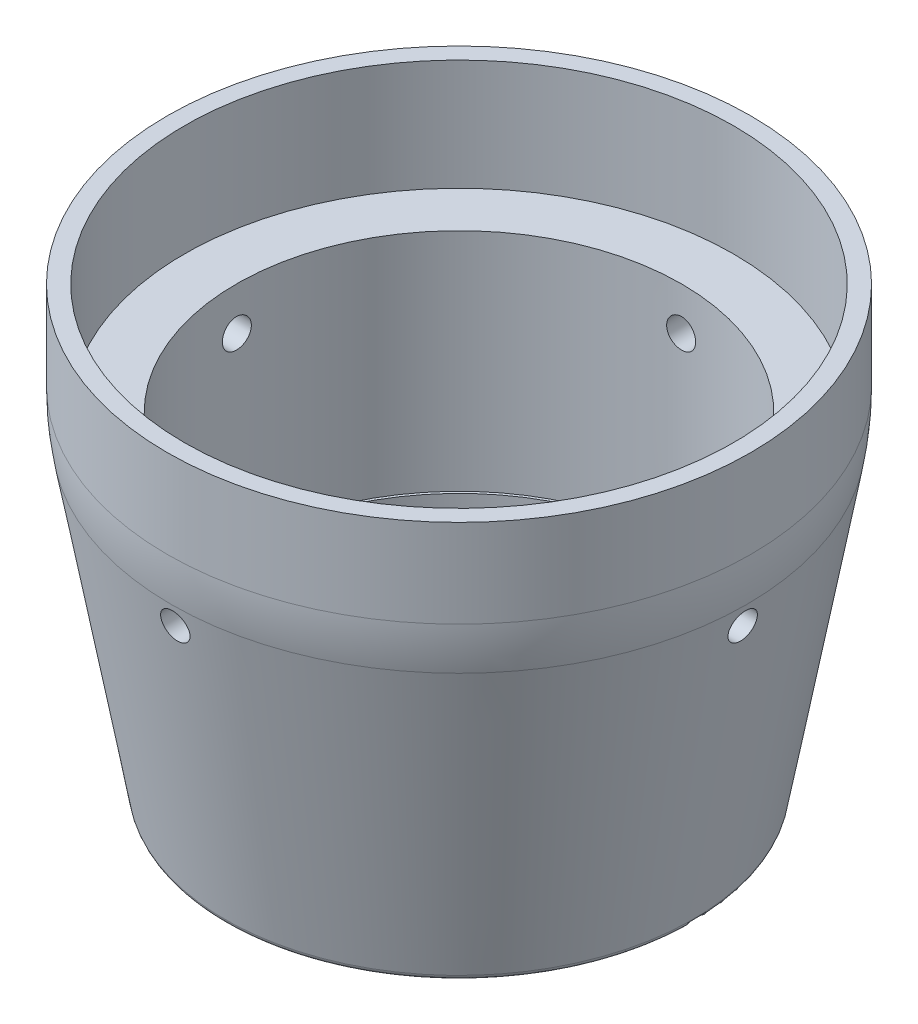
SolidWorks part; units mm, degrees
material "6061-T6 (SS)"
ref_plane "Front Plane" through (0, 0, 0) normal (0, 0, 1) x (1, 0, 0)
ref_plane "Top Plane" through (0, 0, 0) normal (0, 1, 0) x (1, 0, 0)
ref_plane "Right Plane" through (0, 0, 0) normal (1, 0, 0) x (0, 0, -1)
sketch "Sketch2" plane through (0, 0, 0) normal (0, 0, 1) x (1, 0, 0)
  line L8 (22.0472, -22.4282) -> (22.0472, -0.0762)
  line L10 (28.8925, 10.922) -> (28.8925, -0.0762)
  line L11 (28.8925, -0.0762) -> (23.0632, -32.512)
  line L12 (23.0632, -32.512) -> (21.7932, -32.512)
  line L13 (21.7932, -32.512) -> (21.7932, -22.4282)
  line L14 (22.0472, -0.0762) -> (27.1907, -0.0762)
  line L18 (21.7932, -22.4282) -> (22.0472, -22.4282)
  line L19 (27.1907, -0.0762) -> (27.1907, 10.922)
  line L20 (-28.8925, 10.922) -> (28.8925, 10.922) construction
  line L21 (27.1907, 10.922) -> (28.8925, 10.922)
  line L22 (21.717, -32.512) -> (21.717, -22.352) construction
  line L23 (21.971, -22.352) -> (21.971, 7.62) construction
  line L24 (-21.971, -22.352) -> (21.971, -22.352) construction
  line L25 (-27.1145, 0) -> (27.1145, 0) construction
  line L27 (27.1145, 0) -> (27.1145, 10.922) construction
  line L28 (-21.717, -32.512) -> (21.717, -32.512) construction
  dimension "D1" = 0.0762
  dimension "D2" = 0.0762
  dimension "D3" = 0.0762
  dimension "D4" = 0.0762
  dimension "D5" = 0.0762
  dimension "D6" = 1.27
ref_axis "Axis1" through (0, -34.5451, 0) along (0, 1, 0)
revolve "Revolve1" add sketch "Sketch2" angle 360 about axis through (0, -34.5451, 0) along (0, 1, 0)
ref_plane "Plane1" through (0, 0, 28.8925) normal (0, 0, 1) x (1, 0, 0)
sketch "Sketch3" plane through (0, 0, 28.8925) normal (0, 0, 1) x (1, 0, 0)
  line L0 (0, -34.5451) -> (0, 13.0871) construction
  line L2 (28.8925, 10.922) -> (-28.8925, 10.922) construction
  point P0 (0, -4.318)
  dimension "D1" = 15.24
hole_wizard "#6-40 Tapped Hole1" positions "Sketch5" profile "Sketch7" tap size "#6-40" standard "ANSI Inch"
sketch "Sketch5" plane through (0, 0, 28.8925) normal (0, 0, 1) x (1, 0, 0)
  point P0 (0, -4.318)
sketch "Sketch7" plane through (0, -4.318, 28.8925) normal (1, 0, 0) x (0, -1, 0)
  line L0 (0, 0) -> (0, 6.8453)
  line L1 (0, 6.8453) -> (1.4351, 6.8453)
  line L2 (1.4351, 6.8453) -> (1.4351, 0)
  line L5 (1.4351, 0) -> (0, 0)
  line L11 (0, -6.35) -> (0, 107.95) construction
  dimension "Thru Tap Drill Dia." = 2.8702
  dimension "Thru Tap Drill Depth" = 6.8453
pattern_circular "CirPattern1" count 4 over 360 about axis through (0, -34.5451, 0) along (0, -1, 0) of "#6-40 Tapped Hole1"
fillet "Fillet1" radius 0.635 1 edges at (0, -32.512, -23.0632)
fillet "Fillet2" radius 25.4 1 edges at (0, -0.0762, -28.8925)
